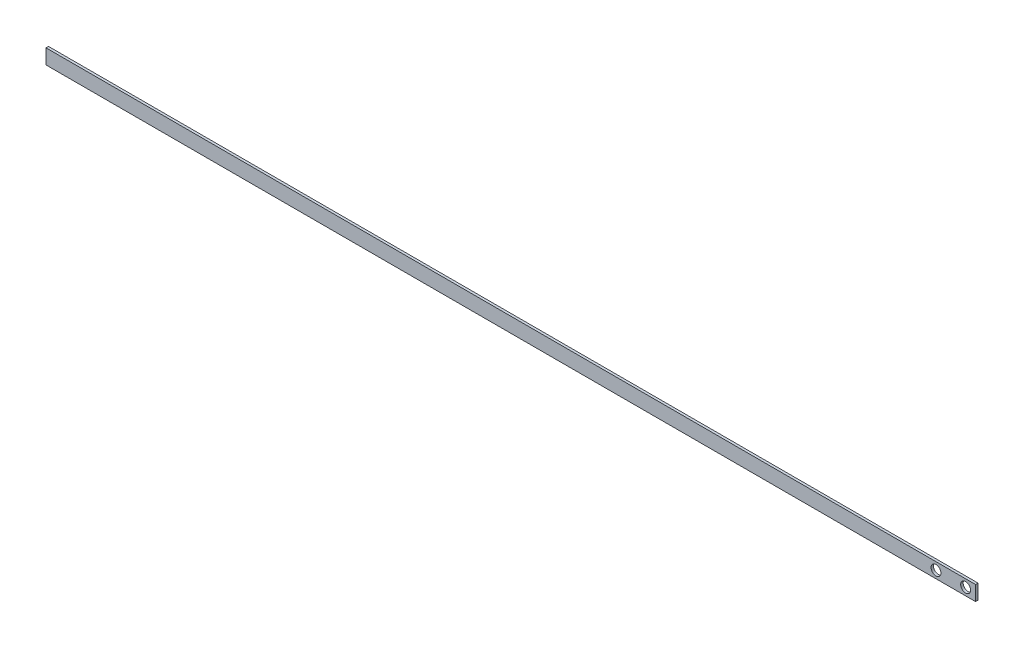
SolidWorks part; units mm, degrees
ref_plane "正面" through (0, 0, 0) normal (0, 0, 1) x (1, 0, 0)
ref_plane "平面" through (0, 0, 0) normal (0, 1, 0) x (1, 0, 0)
ref_plane "右側面" through (0, 0, 0) normal (1, 0, 0) x (0, 0, -1)
sketch "ｽｹｯﾁ1" plane through (0, 0, 0) normal (0, 0, 1) x (1, 0, 0)
  line L1 (0, 0) -> (188, 0)
  line L2 (0, 0) -> (0, -3)
  line L3 (0, -3) -> (188, -3)
  line L4 (188, 0) -> (188, -3)
  dimension "D1" = 188
  dimension "D2" = 3
extrude "ﾎﾞｽ - 押し出し1" add sketch "ｽｹｯﾁ1" along normal blind 0.5
sketch "ｽｹｯﾁ2" plane through (0, 0, 0.5) normal (0, 0, 1) x (1, 0, 0)
  line L0 (0, -1.5) -> (188, -1.5) construction
  line L1 (0, 0) -> (0, -3) construction
  line L2 (188, -3) -> (188, 0) construction
  circle A0 centre (180, -1.5) radius 1
  circle A1 centre (186, -1.5) radius 1
  dimension "D1" = 2
  dimension "D2" = 2
  dimension "D3" = 8
  dimension "D4" = 2
extrude "ｶｯﾄ - 押し出し1" cut sketch "ｽｹｯﾁ2" against normal blind 1
